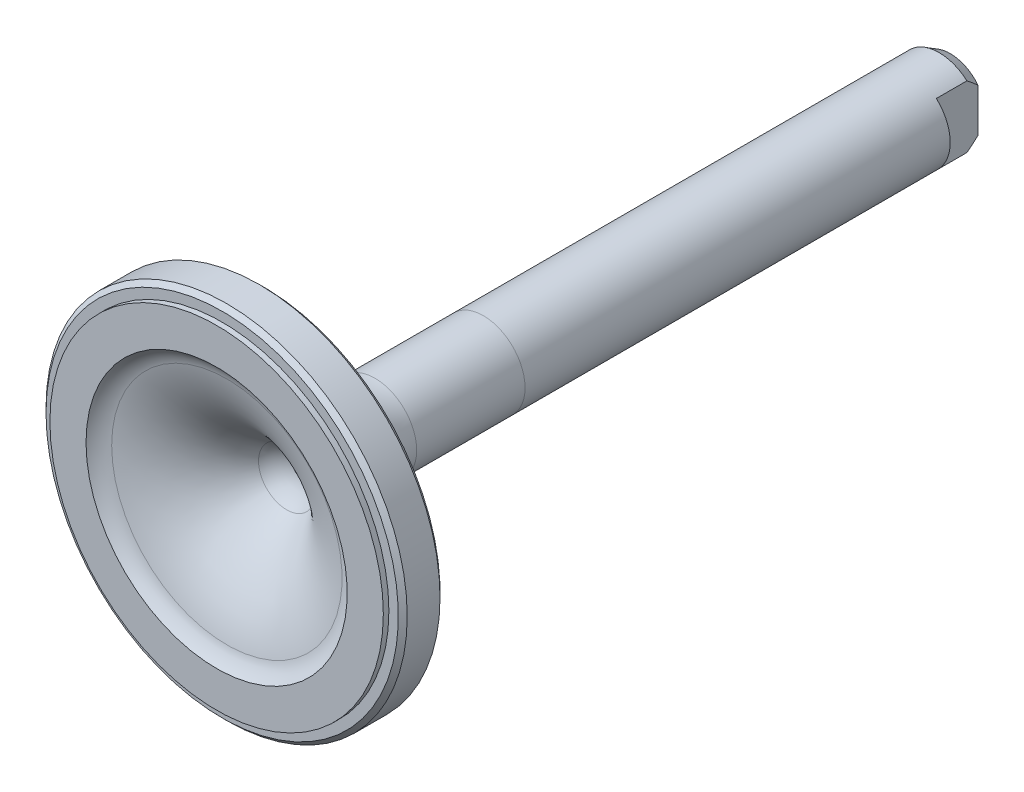
SolidWorks part; units mm, degrees
material "AISI 4340 Steel, normalized"
ref_plane "Plane1" through (0, 0, 0) normal (0, 0, 1) x (1, 0, 0)
ref_plane "Plane2" through (0, 0, 0) normal (0, 1, 0) x (1, 0, 0)
ref_plane "Plane3" through (0, 0, 0) normal (1, 0, 0) x (0, 0, -1)
sketch "Sketch1" plane through (0, 0, 0) normal (0, 0, 1) x (1, 0, 0)
  circle A0 centre (0, 0) radius 41.275
  dimension "D1" = 82.55
extrude "Base-Extrude" add sketch "Sketch1" along normal blind 10.795
sketch "Sketch6" plane through (0, 0, 0) normal (0, 0, -1) x (-1, 0, 0)
  circle A0 centre (0, 0) radius 9.525
  dimension "D1" = 19.05
extrude "Boss-Extrude2" add sketch "Sketch6" along normal blind 156.845
fillet "Fillet1" radius 25.4 1 edges at (9.525, 0, 0)
ref_plane "Plane4" through (0, 0, -178.435) normal (0, 0, 1) x (1, 0, 0)
ref_plane "Plane5" through (0, 0, -0.7937) normal (0, 0, -1) x (-1, 0, 0)
sketch "Sketch9" plane through (0, 0, 0) normal (0, 0, -1) x (-1, 0, 0)
  circle A0 centre (34.925, 0) radius 3.3734
  dimension "D2" = 6.7469
  dimension "D1" = 34.925
extrude "Cut-Extrude2" cut sketch "Sketch9" against normal blind 4.7625 and the other way through all
mirror "Mirror1" about plane through (0, 0, 0) normal (1, 0, 0) of "Cut-Extrude2"
sketch "Sketch26" plane through (0, 0, 10.795) normal (0, 0, 1) x (1, 0, 0)
  circle A0 centre (0, 0) radius 69.0375
  circle A1 centre (0, 0) radius 38.1
  arc A3 (34.7621, 3.3695) -> (-34.7621, 3.3695) centre (0, 0) ccw construction
  dimension "D1" = 76.2
extrude "Cut-Extrude7" cut sketch "Sketch26" against normal blind 1.27
sketch "Sketch19" plane through (0, 0, 0) normal (0, 1, 0) x (1, 0, 0)
  line L0 (-38.1, -10.795) -> (38.1, -10.795) construction
  line L1 (12.7, 156.845) -> (6.35, 156.845)
  line L2 (12.7, 156.845) -> (12.7, 147.32)
  line L3 (12.7, 147.32) -> (6.35, 147.32)
  line L4 (6.35, 156.845) -> (6.35, 147.32)
  line L5 (0, 156.845) -> (0, 25.4) construction
  line L8 (0, -50) -> (0, 50) construction
  dimension "D1" = 9.525
  dimension "D2" = 6.35
  dimension "D3" = 12.7
  dimension "D4" = 167.64
extrude "Cut-Extrude6" cut sketch "Sketch19" against normal through all and the other way through all
mirror "Mirror2" about plane through (0, 0, 0) normal (1, 0, 0) of "Cut-Extrude6"
sketch "Sketch21" plane through (0, 0, 0) normal (0, 1, 0) x (1, 0, 0)
  line L0 (0, -10.795) -> (0, -42.5213) construction
  line L1 (0, -50) -> (0, 50) construction
  line L3 (29.845, -10.795) -> (0, -10.795)
  line L4 (0, -10.795) -> (0, 8.9164)
  line L5 (0, 8.9164) -> (1.5875, 8.9164)
  line L6 (1.5875, 8.9164) -> (1.5875, 8.3737)
  line L7 (-38.1, -10.795) -> (38.1, -10.795) construction
  arc A0 (6.4254, 5.2127) -> (26.3281, -8.4504) centre (34.925, 25.4) ccw
  arc A1 (9.525, 25.4) -> (31.5516, 0.225) centre (34.925, 25.4) ccw construction
  arc A2 (26.3281, -8.4504) -> (29.845, -10.795) centre (24.765, -14.605) cw
  arc A3 (6.4254, 5.2127) -> (1.5875, 8.3737) centre (0, 0.6614) ccw
  dimension "D1" = 34.925
  dimension "D3" = 6.35
  dimension "D4" = 7.874
  dimension "D2" = 3.81
  dimension "D5" = 3.175
  dimension "D6" = 8.255
revolve "Cut-Revolve6" cut sketch "Sketch21" angle 360 about L0
sketch "Sketch22" plane through (0, 0, 0) normal (0, 1, 0) x (1, 0, 0)
  line L0 (0, -10.795) -> (0, 188.0182) construction
  line L2 (8.0585, 156.845) -> (9.525, 156.845)
  line L3 (9.525, 156.845) -> (9.525, 154.305)
  line L4 (9.525, 154.305) -> (8.0585, 156.845)
  line L7 (-38.1, -10.795) -> (38.1, -10.795) construction
  dimension "D1" = 19.05
  dimension "D2" = 30
  dimension "D3" = 2.54
  dimension "D4" = 167.64
sketch "Sketch23" plane through (0, 0, 0) normal (0, 1, 0) x (1, 0, 0)
  line L0 (0, -10.795) -> (0, -51.9211) construction
  line L2 (40.259, 0) -> (41.275, 0)
  line L3 (41.275, 0) -> (41.275, -1.016)
  line L4 (41.275, -1.016) -> (40.259, 0)
  line L5 (40.259, -9.525) -> (41.275, -9.525)
  line L6 (41.275, -9.525) -> (41.275, -8.509)
  line L7 (41.275, -8.509) -> (40.259, -9.525)
  line L12 (-38.1, -10.795) -> (38.1, -10.795) construction
  dimension "D1" = 82.55
  dimension "D2" = 1.016
  dimension "D3" = 1.27
  dimension "D4" = 9.525
revolve "Cut-Revolve7" cut sketch "Sketch22" angle 360 about L0
revolve "Cut-Revolve8" cut sketch "Sketch23" angle 360 about L0
sketch "Sketch27" plane through (0, 0, 0) normal (1, 0, 0) x (0, 0, -1)
  line L0 (50.165, 32.1318) -> (50.165, -30.6411)
  line L1 (-10.795, 38.1) -> (-10.795, -38.1) construction
  dimension "D1" = 60.96
split line "Split Line1"
